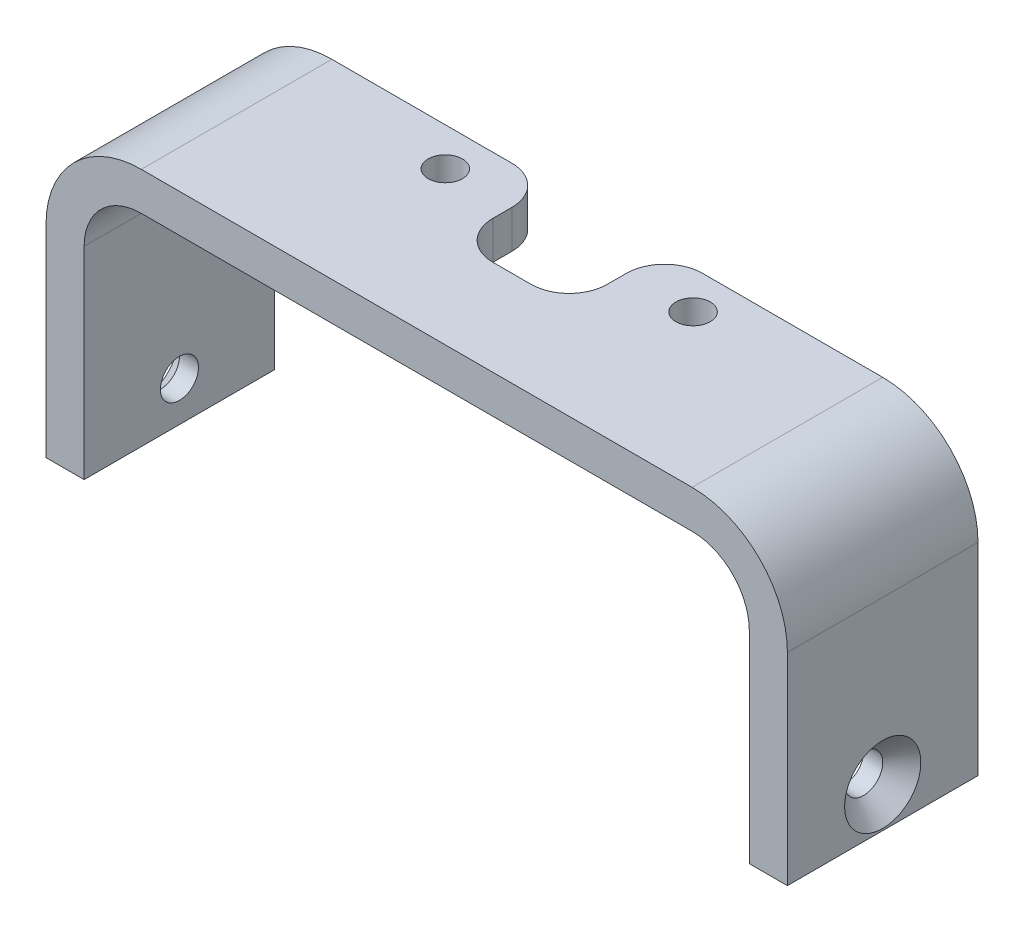
SolidWorks part; units mm, degrees
ref_plane "Front Plane" through (0, 0, 0) normal (0, 0, 1) x (1, 0, 0)
ref_plane "Top Plane" through (0, 0, 0) normal (0, 1, 0) x (1, 0, 0)
ref_plane "Right Plane" through (0, 0, 0) normal (1, 0, 0) x (0, 0, -1)
sketch "Sketch1" plane through (0, 0, 0) normal (0, 0, 1) x (1, 0, 0)
  line L0 (17.45, 0) -> (19.45, 0)
  line L2 (-17.45, 0) -> (-17.45, 10.6)
  line L3 (-14.45, 13.6) -> (14.45, 13.6)
  line L4 (17.45, 0) -> (17.45, 10.6)
  line L5 (-19.45, 0) -> (-17.45, 0)
  line L6 (-19.45, 0) -> (-19.45, 10.6)
  line L7 (-14.45, 15.6) -> (14.45, 15.6)
  line L8 (19.45, 0) -> (19.45, 10.6)
  line L9 (-17.45, 0) -> (17.45, 0) construction
  arc A0 (17.45, 10.6) -> (14.45, 13.6) centre (14.45, 10.6) ccw
  arc A1 (-14.45, 13.6) -> (-17.45, 10.6) centre (-14.45, 10.6) ccw
  arc A2 (19.45, 10.6) -> (14.45, 15.6) centre (14.45, 10.6) ccw
  arc A3 (-14.45, 15.6) -> (-19.45, 10.6) centre (-14.45, 10.6) ccw
  point P8 (0, 0)
  point P12 (17.45, 13.6)
  dimension "D4" = 3
  dimension "D5" = 5
  dimension "D1" = 2
  dimension "D2" = 2
  dimension "D3" = 13.6
  dimension "D6" = 34.9
extrude "Boss-Extrude1" add sketch "Sketch1" along normal blind 10
sketch "Sketch2" plane through (19.45, 0, 0) normal (1, 0, 0) x (0, 0, -1)
  line L0 (-10, 0) -> (0, 0) construction
  circle A0 centre (-5, 2.1) radius 1
  dimension "D1" = 2
  dimension "D2" = 2.1
extrude "Cut-Extrude1" cut sketch "Sketch2" against normal through all and the other way through all
chamfer "Chamfer1" distance 1 angle 45 2 edges at (-19.45, 3.1, 5) (19.45, 2.1, 6)
sketch "Sketch3" plane through (0, 15.6, 0) normal (0, 1, 0) x (1, 0, 0)
  line L0 (-6.5, -2) -> (6.5, -2) construction
  line L1 (14.45, 0) -> (-14.45, 0) construction
  line L3 (3, 0) -> (-3, 0)
  line L4 (3, 0) -> (3, -5)
  line L5 (3, -5) -> (-3, -5)
  line L6 (-3, 0) -> (-3, -5)
  circle A0 centre (-6.5, -2) radius 0.9
  circle A1 centre (6.5, -2) radius 0.9
  point P2 (0, -2)
  point P12 (0, 0)
  dimension "D1" = 1.8
  dimension "D2" = 13
  dimension "D3" = 2
  dimension "D4" = 5
  dimension "D5" = 6
extrude "Cut-Extrude2" cut sketch "Sketch3" against normal through all
fillet "Fillet1" radius 2 4 edges at (3, 14.6, 0) (3, 14.6, 5) (-3, 14.6, 5) (-3, 14.6, 0)
